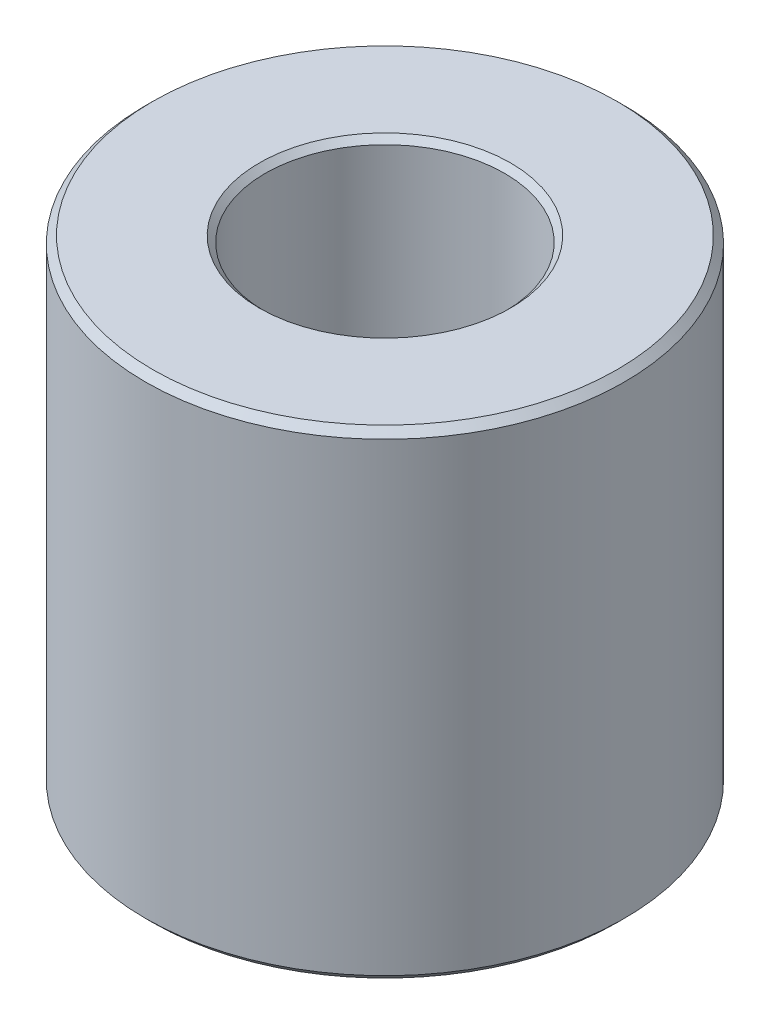
SolidWorks part; units mm, degrees
material "Brass"
ref_plane "Front" through (0, 0, 0) normal (0, 0, 1) x (1, 0, 0)
ref_plane "Top" through (0, 0, 0) normal (0, 1, 0) x (1, 0, 0)
ref_plane "Right" through (0, 0, 0) normal (1, 0, 0) x (0, 0, -1)
sketch "Sketch1" plane through (0, 0, 0) normal (0, 1, 0) x (1, 0, 0)
  circle A0 centre (0, 0) radius 25.4
  dimension "D1" = 50.8
extrude "Extrude1" add sketch "Sketch1" along normal blind 50.8
hole_wizard "1/2 (0.5) Diameter Hole1" positions "Sketch3" profile "Sketch2" hole size "1/2" standard "Ansi Inch" end condition through all
sketch "Sketch3" plane through (0, 50.8, 0) normal (0, 1, 0) x (-1, 0, 0)
  point P0 (0, 0)
sketch "Sketch2" plane through (0, 50.8, 0) normal (1, 0, 0) x (0, 0, 1)
  line L0 (0, 0) -> (0, 50.8)
  line L1 (0, 50.8) -> (6.3627, 50.8)
  line L2 (6.3627, 50.8) -> (6.3627, 0)
  line L5 (6.3627, 0) -> (0, 0)
  line L11 (0, -6.35) -> (0, 107.95) construction
  dimension "Thru Hole Dia." = 12.7254
  dimension "Thru Hole Depth" = 50.8
chamfer "Chamfer1" distance 0.762 angle 45 3 edges at (0, 0, 25.4) (0, 50.8, 25.4) (0, 0, 6.3627)
hole_wizard "1 (1) Diameter Hole1" positions "Sketch5" profile "Sketch4" hole size "1" standard "Ansi Inch"
sketch "Sketch5" plane through (0, 50.8, 0) normal (0, 1, 0) x (-1, 0, 0)
  point P0 (0, 0)
sketch "Sketch4" plane through (0, 50.8, 0) normal (1, 0, 0) x (0, 0, 1)
  line L0 (0, 0) -> (0, 42.926)
  line L1 (0, 42.926) -> (12.7, 42.926)
  line L2 (12.7, 42.926) -> (12.7, 0)
  line L5 (12.7, 0) -> (0, 0)
  line L10 (0, 42.926) -> (-12.7, 42.926) construction
  line L11 (0, -6.35) -> (0, 107.95) construction
  dimension "Hole Dia." = 25.4
  dimension "Hole Depth" = 42.926
  dimension "Drill Angle" = 180
chamfer "Chamfer2" distance 0.254 angle 45 1 edges at (0, 7.874, 12.7)
chamfer "Chamfer3" distance 0.635 angle 45 1 edges at (0, 50.8, 12.7)
